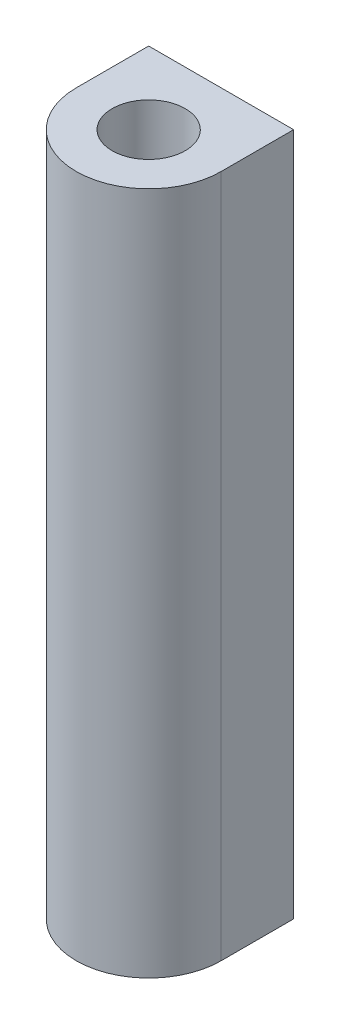
SolidWorks part; units mm, degrees
material "ABS"
ref_plane "X-Y Datum" through (0, 0, 0) normal (0, 0, 1) x (1, 0, 0)
ref_plane "X-Z Datum" through (0, 0, 0) normal (0, 1, 0) x (1, 0, 0)
ref_plane "Y-Z Datum" through (0, 0, 0) normal (1, 0, 0) x (0, 0, -1)
sketch "Sketch1" plane through (0, 0, 0) normal (0, 1, 0) x (1, 0, 0)
  line L0 (-6, 0) -> (-6, 5.43)
  line L1 (-6, 6) -> (6, 6)
  line L2 (6, 5.43) -> (6, 0)
  line L3 (0, 6) -> (0, 5.43) construction
  line L4 (-6, 5.43) -> (6, 5.43) construction
  line L5 (-6, 5.43) -> (-6, 6)
  line L6 (6, 6) -> (6, 5.43)
  arc A0 (-6, 0) -> (6, 0) centre (0, 0) ccw
  circle A1 centre (0, 0) radius 3.025
extrude "Boss-Extrude1" add sketch "Sketch1" along normal blind 56.6 contours A1 | A0 L2 L6 L1 L5 L0
ref_plane "Plane1" through (0, 28.3, 0) normal (0, 1, 0) x (1, 0, 0)
